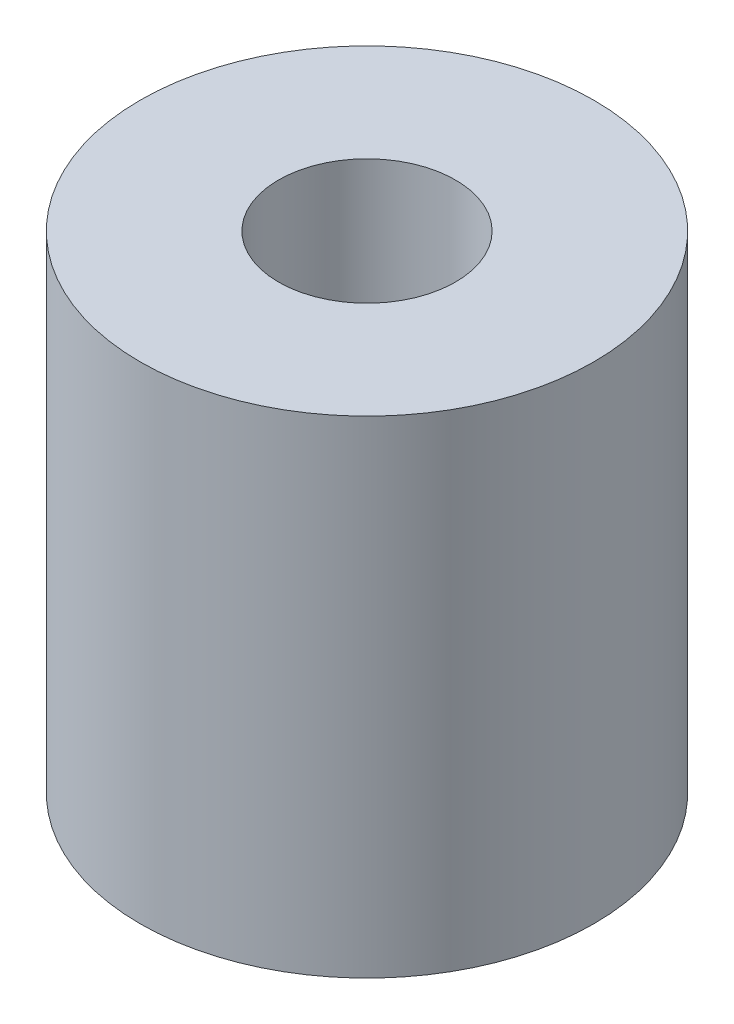
SolidWorks part; units mm, degrees
ref_plane "Front Plane" through (0, 0, 0) normal (0, 0, 1) x (1, 0, 0)
ref_plane "Top Plane" through (0, 0, 0) normal (0, 1, 0) x (1, 0, 0)
ref_plane "Right Plane" through (0, 0, 0) normal (1, 0, 0) x (0, 0, -1)
sketch "Sketch1" plane through (0, 0, 0) normal (0, 1, 0) x (1, 0, 0)
  circle A0 centre (0, 0) radius 41
  circle A1 centre (0, 0) radius 16
  dimension "D1" = 82
  dimension "D2" = 32
extrude "Boss-Extrude1" add sketch "Sketch1" along normal blind 88
